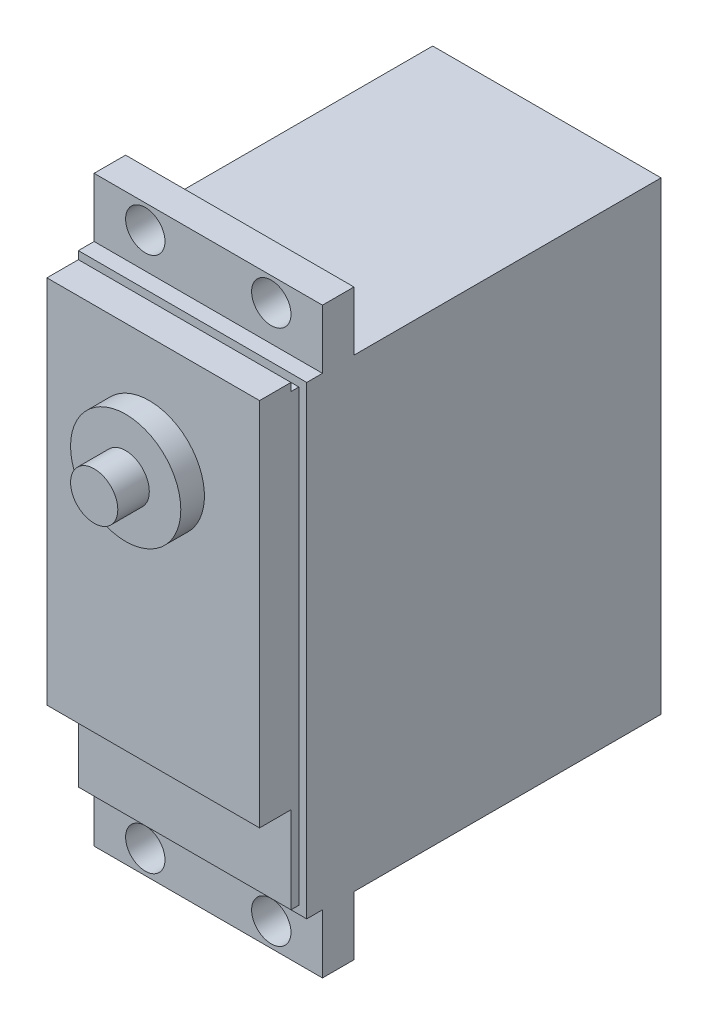
SolidWorks part; units mm, degrees
material "Nylon 101"
ref_plane "Front Plane" through (0, 0, 0) normal (0, 0, 1) x (1, 0, 0)
ref_plane "Top Plane" through (0, 0, 0) normal (0, 1, 0) x (1, 0, 0)
ref_plane "Right Plane" through (0, 0, 0) normal (1, 0, 0) x (0, 0, -1)
sketch "Sketch4" plane through (0, 0, 0) normal (0, 0, 1) x (1, 0, 0)
  line L1 (-59.13, 19.3991) -> (-30.13, 19.3991)
  line L2 (-59.13, 19.3991) -> (-59.13, -39.6009)
  line L3 (-59.13, -39.6009) -> (-30.13, -39.6009)
  line L4 (-30.13, 19.3991) -> (-30.13, -39.6009)
extrude "Boss-Extrude2" add sketch "Sketch4" along normal blind 43
sketch "Sketch5" plane through (0, 0, 43) normal (0, 0, 1) x (1, 0, 0)
  line L0 (-59.13, 19.3991) -> (-59.13, -39.6009) construction
  line L1 (-59.13, -47.1009) -> (-30.13, -47.1009)
  line L2 (-59.13, -47.1009) -> (-59.13, 26.8991)
  line L3 (-59.13, 26.8991) -> (-30.13, 26.8991)
  line L4 (-30.13, -47.1009) -> (-30.13, 26.8991)
  line L5 (-30.13, 19.3991) -> (-59.13, 19.3991) construction
  line L6 (-30.13, -39.6009) -> (-30.13, 19.3991) construction
  line L7 (-59.13, -39.6009) -> (-30.13, -39.6009) construction
  dimension "D1" = 0
  dimension "D2" = 7.5
  dimension "D3" = 0
  dimension "D4" = 7.5
extrude "Boss-Extrude3" add sketch "Sketch5" against normal blind 4
sketch "Sketch6" plane through (0, 0, 43) normal (0, 0, 1) x (1, 0, 0)
  line L0 (-59.13, 26.8991) -> (-59.13, -47.1009) construction
  line L1 (-59.13, 19.3991) -> (-30.13, 19.3991)
  line L2 (-59.13, 19.3991) -> (-59.13, -39.6009)
  line L3 (-59.13, -39.6009) -> (-30.13, -39.6009)
  line L4 (-30.13, 19.3991) -> (-30.13, -39.6009)
  line L5 (-30.13, -47.1009) -> (-30.13, 26.8991) construction
  line L6 (-30.13, 26.8991) -> (-59.13, 26.8991) construction
  dimension "D1" = 7.5
  dimension "D2" = 59
extrude "Boss-Extrude4" add sketch "Sketch6" along normal blind 2
sketch "Sketch7" plane through (0, 0, 45) normal (0, 0, 1) x (1, 0, 0)
  line L0 (-59.13, 19.3991) -> (-59.13, -39.6009) construction
  line L1 (-58.13, 18.3991) -> (-31.13, 18.3991)
  line L2 (-58.13, 18.3991) -> (-58.13, -38.6009)
  line L3 (-58.13, -38.6009) -> (-31.13, -38.6009)
  line L4 (-31.13, 18.3991) -> (-31.13, -38.6009)
  line L5 (-59.13, -39.6009) -> (-30.13, -39.6009) construction
  dimension "D1" = 57
  dimension "D2" = 27
  dimension "D3" = 1
  dimension "D4" = 1
extrude "Boss-Extrude5" add sketch "Sketch7" along normal blind 1
sketch "Sketch8" plane through (0, 0, 46) normal (0, 0, 1) x (1, 0, 0)
  line L0 (-58.13, 18.3991) -> (-58.13, -38.6009) construction
  line L1 (-58.13, -27.6009) -> (-31.13, -27.6009)
  line L2 (-58.13, -27.6009) -> (-58.13, 19.3991)
  line L3 (-58.13, 19.3991) -> (-31.13, 19.3991)
  line L4 (-31.13, -27.6009) -> (-31.13, 19.3991)
  line L5 (-31.13, -38.6009) -> (-31.13, 18.3991) construction
  line L6 (-59.13, -39.6009) -> (-30.13, -39.6009) construction
  line L7 (-30.13, 19.3991) -> (-59.13, 19.3991) construction
  dimension "D1" = 12
  dimension "D2" = 0
extrude "Boss-Extrude7" add sketch "Sketch8" along normal blind 3.99
sketch "Sketch11" plane through (0, 0, 49.99) normal (0, 0, 1) x (1, 0, 0)
  line L0 (-30.13, 19.3991) -> (-59.13, 19.3991) construction
  line L3 (-59.13, 19.3991) -> (-59.13, -39.6009) construction
  circle A0 centre (-45.13, 5.3991) radius 7
  dimension "D1" = 14
  dimension "D2" = 14
  dimension "D3" = 14
extrude "Boss-Extrude8" add sketch "Sketch11" along normal blind 3
sketch "Sketch12" plane through (0, 0, 52.99) normal (0, 0, 1) x (1, 0, 0)
  circle A0 centre (-45.13, 5.3991) radius 3
extrude "Boss-Extrude9" add sketch "Sketch12" along normal blind 4
sketch "Sketch13" plane through (0, 0, 43) normal (0, 0, 1) x (1, 0, 0)
  line L0 (-30.13, 19.3991) -> (-30.13, 26.8991) construction
  line L1 (-30.13, 26.8991) -> (-59.13, 26.8991) construction
  circle A0 centre (-36.63, 23.8991) radius 2.5
  circle A1 centre (-52.63, 23.8991) radius 2.5
  circle A2 centre (-52.63, -44.1009) radius 2.5
  circle A3 centre (-36.63, -44.1009) radius 2.5
  dimension "D1" = 6.5
  dimension "D2" = 3
  dimension "D3" = 2
  dimension "D4" = 2
extrude "Cut-Extrude1" cut sketch "Sketch13" against normal blind 4
